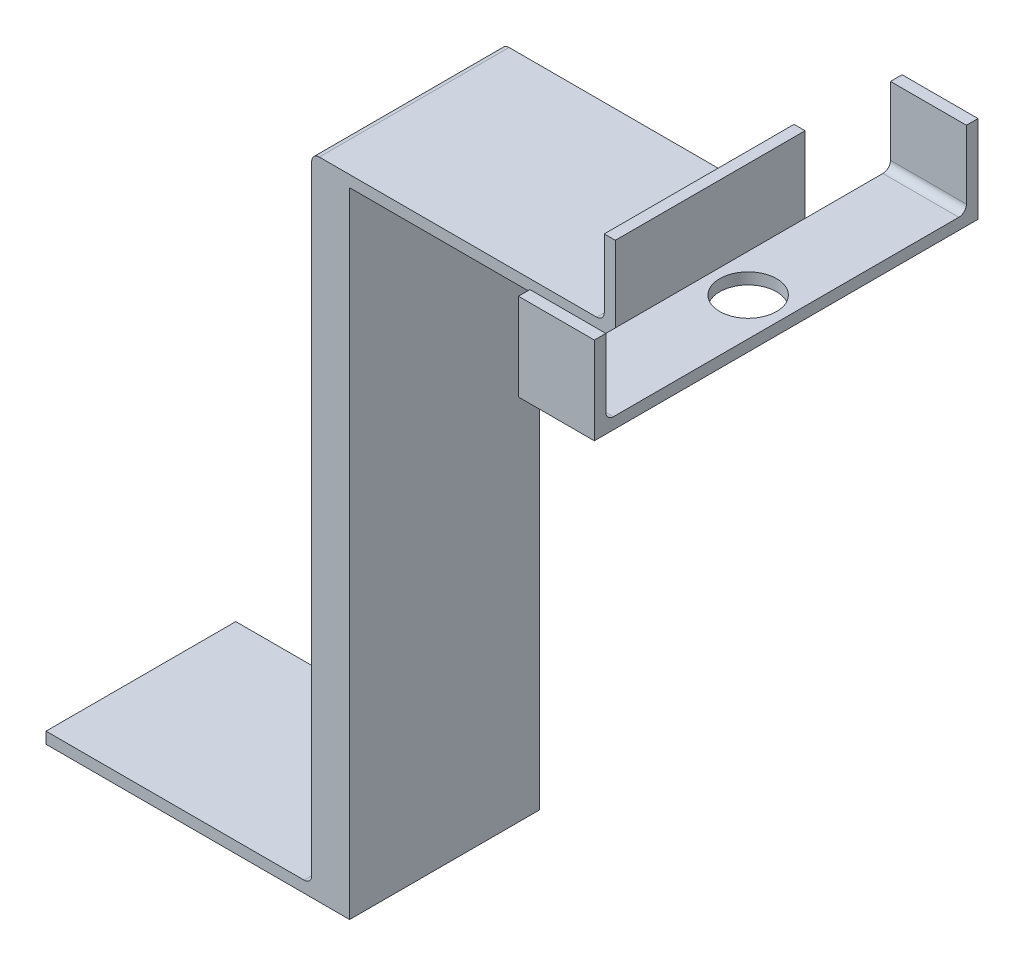
SolidWorks part; units mm, degrees
ref_plane "Front Plane" through (0, 0, 0) normal (0, 0, 1) x (1, 0, 0)
ref_plane "Top Plane" through (0, 0, 0) normal (0, 1, 0) x (1, 0, 0)
ref_plane "Right Plane" through (0, 0, 0) normal (1, 0, 0) x (0, 0, -1)
sketch "Sketch1" plane through (0, 0, 0) normal (0, 1, 0) x (1, 0, 0)
  line L1 (0, 0) -> (101.6, 0)
  line L2 (0, 0) -> (0, -63.5)
  line L3 (0, -63.5) -> (101.6, -63.5)
  line L4 (101.6, 0) -> (101.6, -63.5)
  dimension "D1" = 101.6
  dimension "D2" = 63.5
extrude "Boss-Extrude1" add sketch "Sketch1" along normal blind 3.81
sketch "Sketch2" plane through (0, 3.81, 0) normal (0, 1, 0) x (1, 0, 0)
  line L0 (0, -63.5) -> (101.6, -63.5) construction
  line L1 (101.6, 0) -> (88.9, 0)
  line L2 (101.6, 0) -> (101.6, -63.5)
  line L3 (101.6, -63.5) -> (88.9, -63.5)
  line L4 (88.9, 0) -> (88.9, -63.5)
  dimension "D1" = 12.7
extrude "Boss-Extrude2" add sketch "Sketch2" along normal blind 212.09
sketch "Sketch3" plane through (0, 215.9, 0) normal (0, 1, 0) x (1, 0, 0)
  line L0 (101.6, 0) -> (190.5, 0)
  line L2 (101.6, 0) -> (101.6, -63.5)
  line L5 (101.6, -63.5) -> (190.5, -63.5)
  line L7 (203.2, 28.575) -> (190.5, 28.575)
  line L8 (203.2, 28.575) -> (215.9, 28.575)
  line L9 (203.2, -92.075) -> (215.9, -92.075)
  line L10 (203.2, -92.075) -> (190.5, -92.075)
  line L11 (190.5, 28.575) -> (190.5, 0)
  line L12 (215.9, 28.575) -> (215.9, -92.075)
  line L13 (190.5, -92.075) -> (190.5, -63.5)
  circle A0 centre (203.2, -31.75) radius 9.525
  dimension "D1" = 19.05
  dimension "D5" = 12.7
  dimension "D6" = 12.7
  dimension "D7" = 12.7
  dimension "D8" = 12.7
extrude "Boss-Extrude3" add sketch "Sketch3" against normal blind 3.81
sketch "Sketch4" plane through (0, 215.9, 0) normal (0, 1, 0) x (1, 0, 0)
  line L0 (190.5, -92.075) -> (215.9, -92.075)
  line L1 (215.9, -92.075) -> (215.9, -95.9161)
  line L2 (215.9, -95.9161) -> (190.5, -95.9161)
  line L3 (190.5, -95.9161) -> (190.5, -92.075)
  line L4 (190.5, 0) -> (190.5, -63.5)
  line L5 (190.5, -63.5) -> (186.7991, -63.5)
  line L6 (88.9, -63.5) -> (190.5, -63.5) construction
  line L7 (186.7991, -63.5) -> (186.7991, 0)
  line L8 (190.5, 0) -> (88.9, 0) construction
  line L9 (186.7991, 0) -> (190.5, 0)
  line L12 (215.9, 28.575) -> (190.5, 28.575)
  line L13 (215.9, 28.575) -> (215.9, 32.4607)
  line L14 (215.9, 32.4607) -> (190.5, 32.4607)
  line L15 (190.5, 28.575) -> (190.5, 32.4607)
extrude "Boss-Extrude6" add sketch "Sketch4" along normal blind 25.4
sketch "Sketch6" plane through (0, 215.9, 0) normal (0, -1, 0) x (1, 0, 0)
  line L1 (215.9, -32.4607) -> (190.5, -32.4607)
  line L2 (215.9, -32.4607) -> (215.9, -28.575)
  line L3 (215.9, -28.575) -> (190.5, -28.575)
  line L4 (190.5, -32.4607) -> (190.5, -28.575)
  line L5 (190.5, 95.9161) -> (215.9, 95.9161)
  line L6 (190.5, 95.9161) -> (190.5, 92.075)
  line L7 (190.5, 92.075) -> (215.9, 92.075)
  line L8 (215.9, 95.9161) -> (215.9, 92.075)
extrude "Boss-Extrude7" add sketch "Sketch6" along normal blind 3.81
fillet "Fillet2" radius 2.54 5 edges at (203.2, 215.9, -28.575) (88.9, 215.9, 31.75) (88.9, 3.81, 31.75) (186.7991, 215.9, 31.75) (203.2, 215.9, 92.075)
